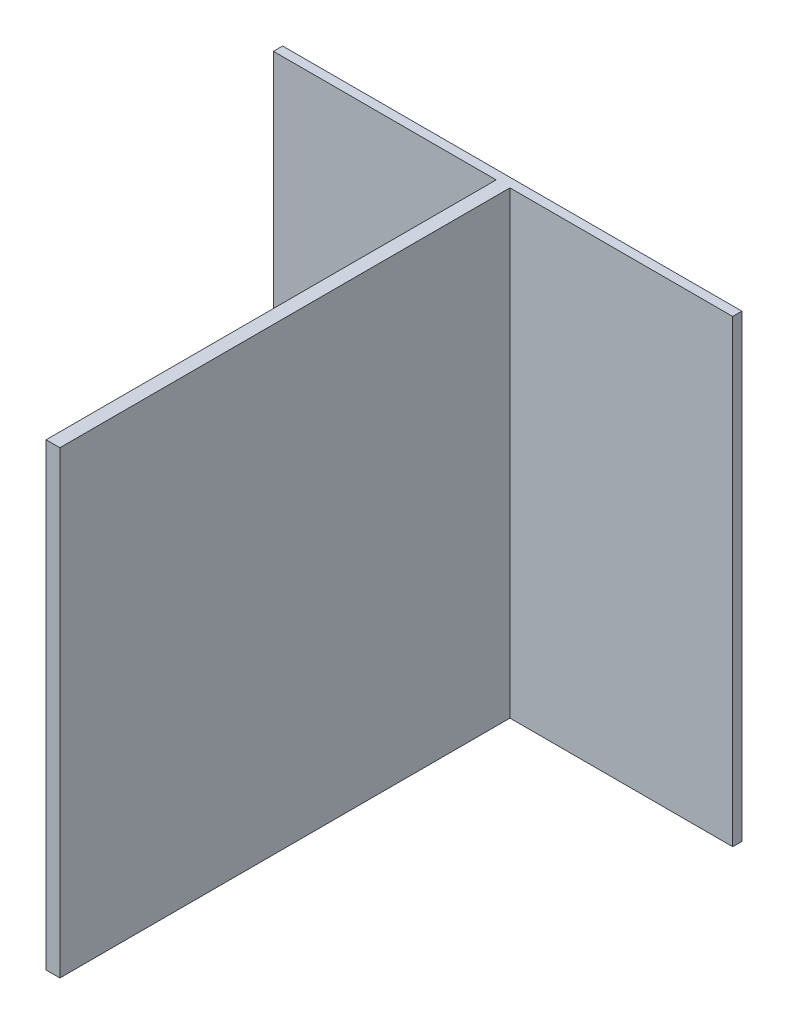
SolidWorks part; units mm, degrees
ref_plane "Płaszczyzna przednia" through (0, 0, 0) normal (0, 0, 1) x (1, 0, 0)
ref_plane "Płaszczyzna górna" through (0, 0, 0) normal (0, 1, 0) x (1, 0, 0)
ref_plane "Płaszczyzna prawa" through (0, 0, 0) normal (1, 0, 0) x (0, 0, -1)
sketch "Szkic1" plane through (0, 0, 0) normal (0, 0, 1) x (1, 0, 0)
  line L0 (0, 0) -> (100, 0)
  line L1 (0, 0) -> (-100, 0)
  line L2 (0, 0) -> (0, 100)
  line L3 (0, 0) -> (0, -100)
  line L4 (0, 100) -> (100, 100)
  line L5 (100, 100) -> (100, 0)
  line L6 (100, -100) -> (0, -100)
  line L7 (100, 0) -> (100, -100)
  line L8 (0, 100) -> (-100, 100)
  line L9 (-100, 100) -> (-100, 0)
  line L10 (-100, -100) -> (-100, 0)
  line L11 (0, -100) -> (-100, -100)
  dimension "D1" = 100
  dimension "D2" = 100
  dimension "D3" = 100
  dimension "D4" = 100
  dimension "D5" = 100
  dimension "D6" = 100
  dimension "D7" = 100
  dimension "D8" = 100
  dimension "D9" = 100
  dimension "D10" = 100
  dimension "D11" = 100
extrude "Dodanie-wyciągnięcie1" add sketch "Szkic1" along normal blind 4 contours L8 L9 L1 L2 | L5 L4 L2 L0 | L7 L0 L3 L6 | L11 L3 L1 L10
sketch "Szkic2" plane through (0, 0, 4) normal (0, 0, 1) x (1, 0, 0)
  line L0 (0, 100) -> (0, -100)
  line L1 (100, 100) -> (-100, 100) construction
  line L2 (100, -100) -> (-100, -100) construction
  line L3 (0, 0) -> (3, 0)
  line L4 (0, 0) -> (-3, 0)
  line L5 (3, 0) -> (3, 100)
  line L6 (3, 100) -> (3, -100)
  line L7 (-3, 0) -> (-3, 100)
  line L8 (-3, 0) -> (-3, -100)
  line L9 (-3, -100) -> (3, -100)
  line L10 (3, 100) -> (-3, 100)
  line M9 (-100, -100) -> (100, -100)
  line M11 (100, 100) -> (-100, 100)
  dimension "D1" = 3
  dimension "D2" = 3
  dimension "D3" = 6
  dimension "D4" = 100
  dimension "D5" = 100
  dimension "D6" = 100
  dimension "D7" = 200
  dimension "D8" = 6
extrude "Dodanie-wyciągnięcie2" add sketch "Szkic2" along normal blind 196 contours L7 L4 L0 M11 | L3 L5 L0 M11 | L4 L8 L0 M9 | L6 L3 L0 M9
